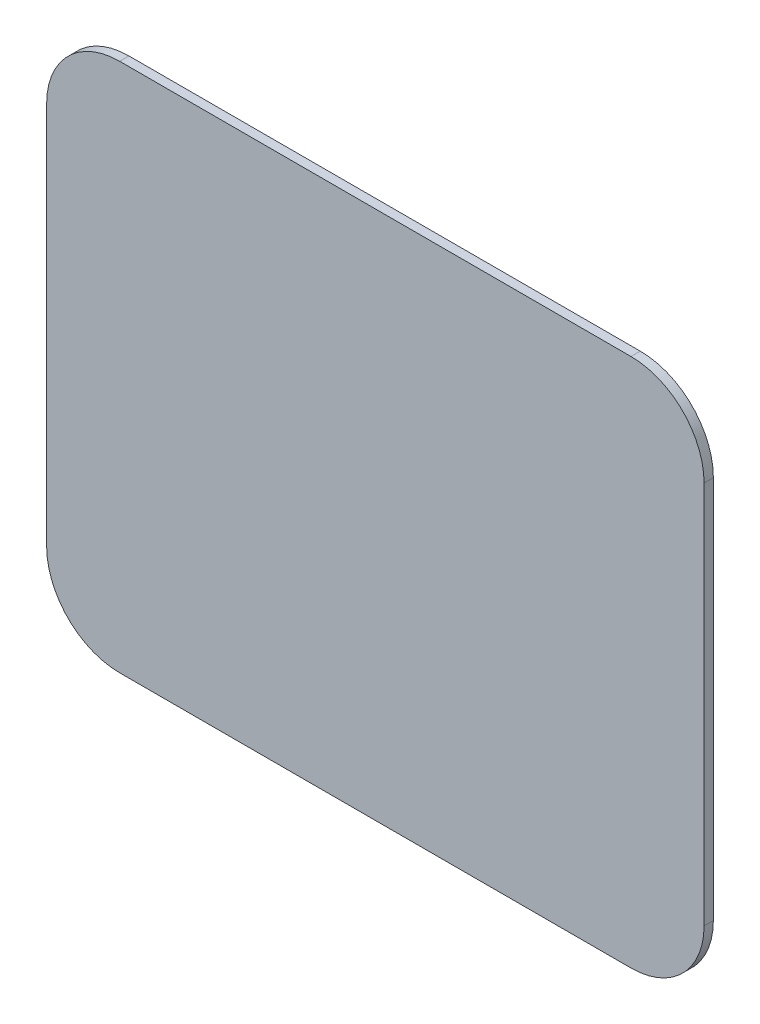
SolidWorks part; units mm, degrees
ref_plane "Front" through (0, 0, 0) normal (0, 0, 1) x (1, 0, 0)
ref_plane "Top" through (0, 0, 0) normal (0, 1, 0) x (1, 0, 0)
ref_plane "Right" through (0, 0, 0) normal (1, 0, 0) x (0, 0, -1)
sketch "Sketch1" plane through (0, 0, 0) normal (0, 0, 1) x (1, 0, 0)
  line L0 (18, -14.5) -> (-18, 14.5) construction
  line L1 (-18, 14.5) -> (18, 14.5)
  line L2 (-18, 14.5) -> (-18, -14.5)
  line L3 (-18, -14.5) -> (18, -14.5)
  line L4 (18, 14.5) -> (18, -14.5)
  dimension "D1" = 36
  dimension "D2" = 29
extrude "Boss-Extrude1" add sketch "Sketch1" along normal blind 0.508
fillet "Fillet1" radius 4 4 edges at (-18, -14.5, 0.254) (18, -14.5, 0.254) (18, 14.5, 0.254) (-18, 14.5, 0.254)
